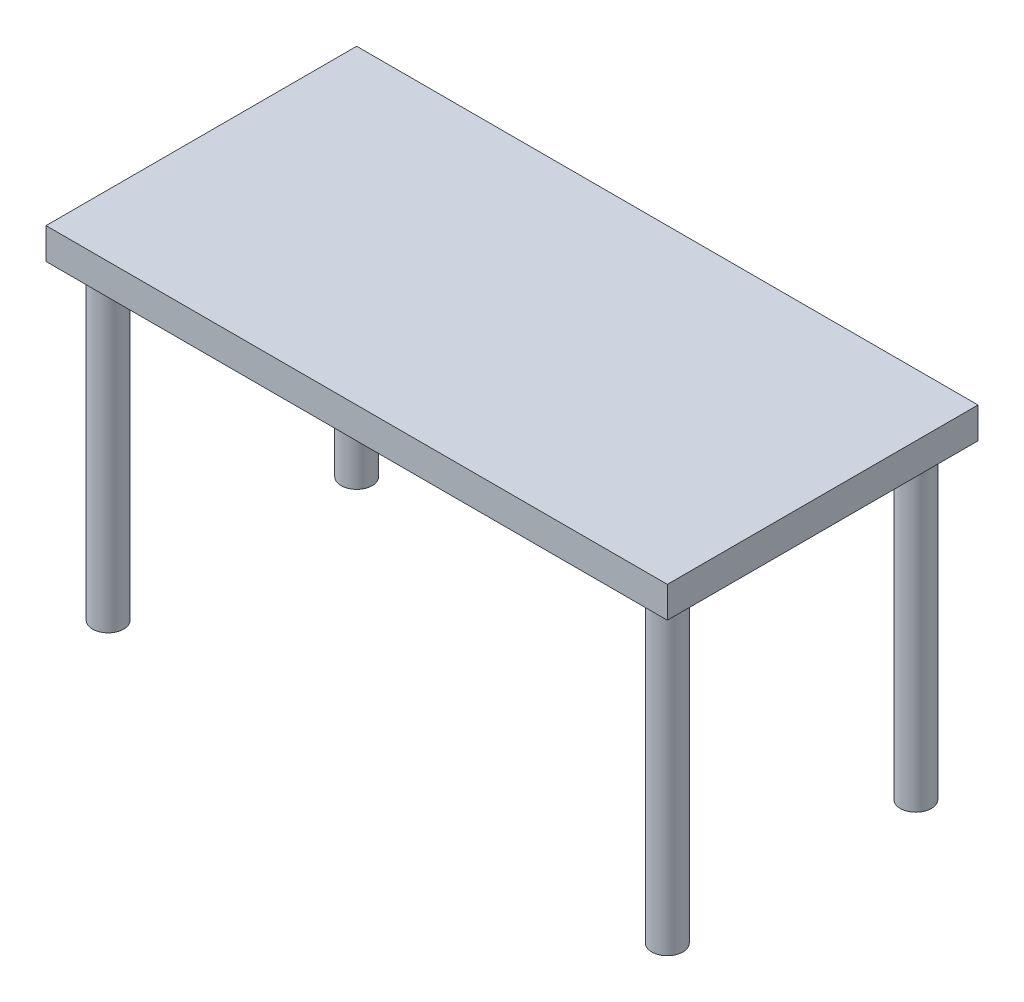
SolidWorks part; units mm, degrees
ref_plane "Front Plane" through (0, 0, 0) normal (0, 0, 1) x (1, 0, 0)
ref_plane "Top Plane" through (0, 0, 0) normal (0, 1, 0) x (1, 0, 0)
ref_plane "Right Plane" through (0, 0, 0) normal (1, 0, 0) x (0, 0, -1)
sketch "Sketch1" plane through (0, 0, 0) normal (0, 1, 0) x (1, 0, 0)
  line L1 (0, 0) -> (1000, 0)
  line L2 (0, 0) -> (0, 500)
  line L3 (0, 500) -> (1000, 500)
  line L4 (1000, 0) -> (1000, 500)
  dimension "D1" = 1000
  dimension "D2" = 500
extrude "Boss-Extrude1" add sketch "Sketch1" against normal blind 100
sketch "Sketch2" plane through (0, -100, 0) normal (0, -1, 0) x (1, 0, 0)
  line L0 (1000, -500) -> (0, -500) construction
  line L1 (1000, 0) -> (1000, -500) construction
  circle A0 centre (900, -400) radius 50
  dimension "D1" = 100
  dimension "D2" = 100
  dimension "D3" = 100
extrude "Boss-Extrude2" add sketch "Sketch2" along normal blind 1000
mirror "Mirror1" about plane through (0, 0, 0) normal (1, 0, 0) of "Boss-Extrude1", "Boss-Extrude2"
mirror "Mirror2" about plane through (0, 0, 0) normal (0, 0, 1) of "Boss-Extrude2", "Boss-Extrude1", "Mirror1"
